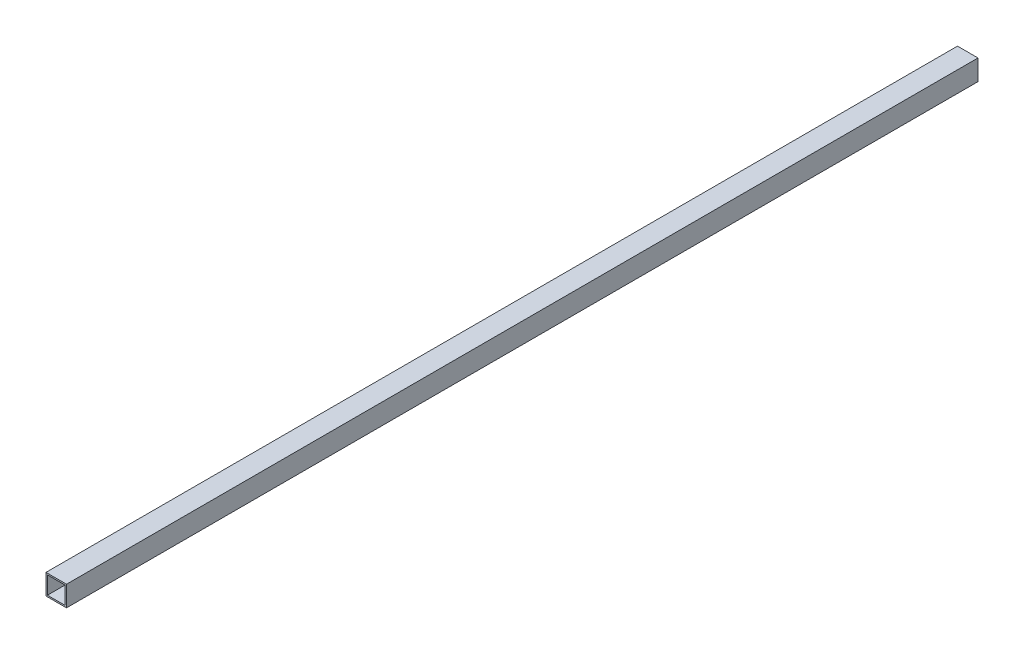
SolidWorks part; units mm, degrees
material "6061 Alloy"
ref_plane "Front Plane" through (0, 0, 0) normal (0, 0, 1) x (1, 0, 0)
ref_plane "Top Plane" through (0, 0, 0) normal (0, 1, 0) x (1, 0, 0)
ref_plane "Right Plane" through (0, 0, 0) normal (1, 0, 0) x (0, 0, -1)
sketch "Sketch1" plane through (0, 0, 0) normal (0, 0, 1) x (1, 0, 0)
  line L0 (-19.05, -19.05) -> (-19.05, 19.05)
  line L1 (-22.225, -22.225) -> (22.225, -22.225)
  line L2 (-22.225, -22.225) -> (-22.225, 22.225)
  line L3 (-22.225, 22.225) -> (22.225, 22.225)
  line L4 (22.225, -22.225) -> (22.225, 22.225)
  line L5 (-22.225, -22.225) -> (22.225, 22.225) construction
  line L6 (-22.225, 22.225) -> (22.225, -22.225) construction
  line L7 (-19.05, 19.05) -> (19.05, 19.05)
  line L8 (19.05, -19.05) -> (19.05, 19.05)
  line L9 (-19.05, -19.05) -> (19.05, -19.05)
  point P0 (0, 0)
  dimension "D1" = 44.45
  dimension "D2" = 44.45
  dimension "D3" = 3.175
extrude "Boss-Extrude1" add sketch "Sketch1" along normal blind 1974.85
